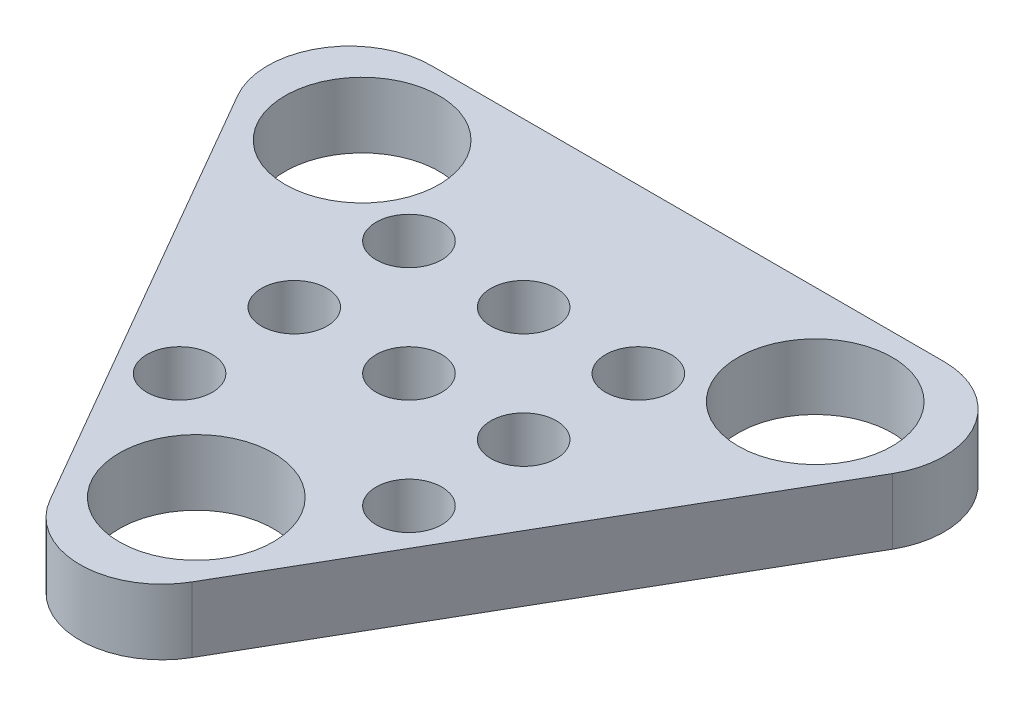
SolidWorks part; units mm, degrees
material "Chrome Stainless Steel"
ref_plane "Front Plane" through (0, 0, 0) normal (0, 0, 1) x (1, 0, 0)
ref_plane "Top Plane" through (0, 0, 0) normal (0, 1, 0) x (1, 0, 0)
ref_plane "Right Plane" through (0, 0, 0) normal (1, 0, 0) x (0, 0, -1)
sketch "Sketch1" plane through (0, 0, 0) normal (0, 1, 0) x (1, 0, 0)
  line L0 (-5.186, 3.3162) -> (2.6377, -10.235)
  line L1 (6.9679, -10.235) -> (14.7916, 3.3162)
  line L2 (12.6266, 7.0662) -> (-3.021, 7.0662)
  line L3 (-1.2742, -3.4594) -> (15.2246, 6.0662) construction
  line L4 (4.8028, 7.0662) -> (4.8028, -11.985) construction
  line L5 (10.8797, -3.4594) -> (-5.6191, 6.0662) construction
  circle A0 centre (-2.1106, 4.0406) radius 2.35
  circle A4 centre (4.8028, -7.9338) radius 2.35
  circle A5 centre (11.7162, 4.0406) radius 2.35
  circle A6 centre (1.2703, 2.0886) radius 1
  circle A7 centre (4.7703, 2.0886) radius 1
  circle A8 centre (8.2703, 2.0886) radius 1
  circle A9 centre (1.2703, -1.4114) radius 1
  circle A10 centre (4.7703, -1.4114) radius 1
  circle A11 centre (8.2703, -1.4114) radius 1
  circle A12 centre (1.2703, -4.9114) radius 1
  circle A13 centre (4.7703, -4.9114) radius 1 [skipped]
  circle A14 centre (8.2703, -4.9114) radius 1
  arc A15 (-5.186, 3.3162) -> (-3.021, 7.0662) centre (-3.021, 4.5662) cw
  arc A16 (14.7916, 3.3162) -> (12.6266, 7.0662) centre (12.6266, 4.5662) ccw
  arc A17 (6.9679, -10.235) -> (2.6377, -10.235) centre (4.8028, -8.985) cw
  point P9 (-7.3511, 7.0662)
  point P12 (4.8028, -13.985)
  point P22 (4.8028, 0.0491)
  dimension "D1" = 4.7
  dimension "D9" = 4.7
  dimension "D10" = 4.7
  dimension "D11" = 2
  dimension "D12" = 2.5
  dimension "D2" = 300
  dimension "D3" = 60
  dimension "D4" = 24.3078
  dimension "D6" = 15
  dimension "D7" = 15
  dimension "D8" = 15
extrude "Extrude1" add sketch "Sketch1" along normal blind 2
